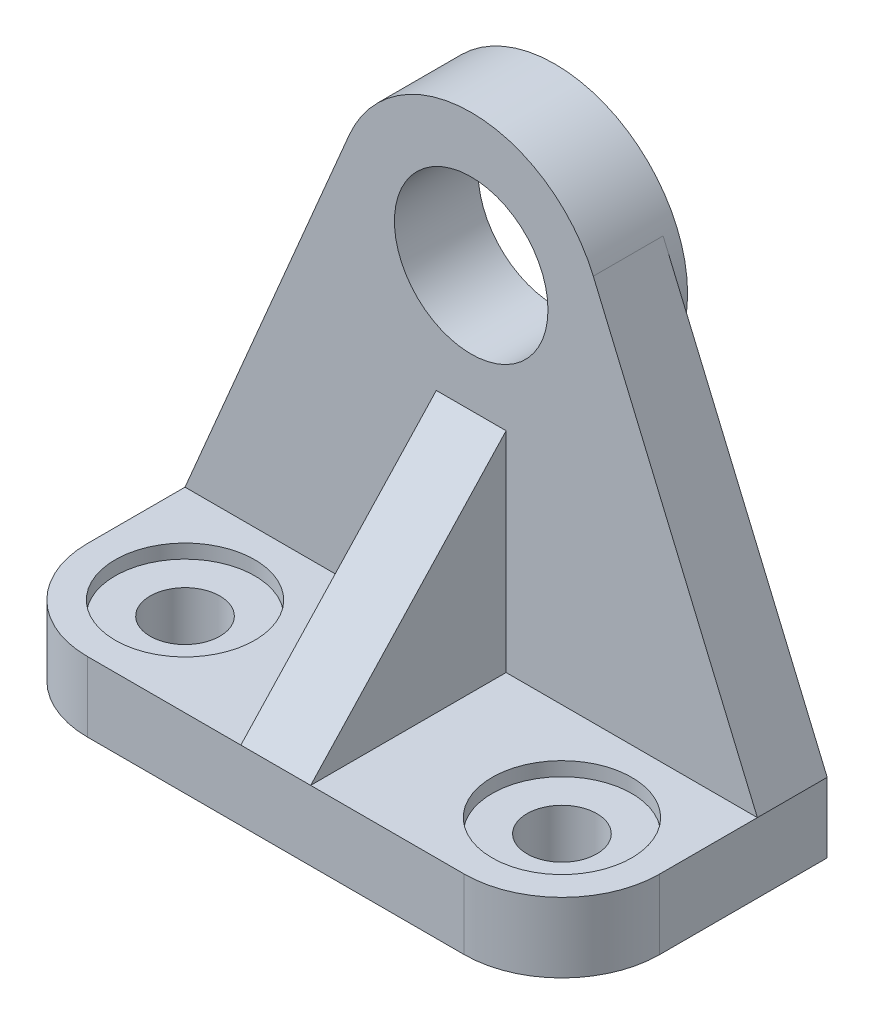
SolidWorks part; units mm, degrees
material "회주철"
ref_plane "정면" through (0, 0, 0) normal (0, 0, 1) x (1, 0, 0)
ref_plane "윗면" through (0, 0, 0) normal (0, 1, 0) x (1, 0, 0)
ref_plane "우측면" through (0, 0, 0) normal (1, 0, 0) x (0, 0, -1)
sketch "스케치1" plane through (0, 0, 0) normal (1, 0, 0) x (0, 0, -1)
  line L0 (0, 0) -> (38, 0)
  line L1 (38, 0) -> (38, 77)
  line L2 (0, 10) -> (28, 10)
  line L3 (28, 10) -> (28, 77)
  line L4 (28, 77) -> (38, 77)
  line L5 (0, 10) -> (0, 0)
  dimension "D1" = 38
  dimension "D2" = 10
  dimension "D3" = 77
extrude "보스-돌출1" add sketch "스케치1" along normal mid plane 82
sketch "스케치2" plane through (0, 0, -28) normal (0, 0, 1) x (1, 0, 0)
  line L0 (-41, 77) -> (-41, 10) construction
  line L1 (-41, 10) -> (-17.4914, 65.4197)
  line L2 (17.4914, 65.4197) -> (41, 10)
  line L3 (-41, 10) -> (-41, 77)
  line L4 (-41, 77) -> (41, 77)
  line L5 (41, 77) -> (41, 10)
  circle A0 centre (0, 58) radius 11
  arc A1 (17.4914, 65.4197) -> (-17.4914, 65.4197) centre (0, 58) ccw
  line M3 (-41, 77) -> (-41, 10)
  line M5 (41, 10) -> (41, 77)
  line M6 (41, 77) -> (-41, 77)
  dimension "D1" = 22
  dimension "D2" = 19
extrude "컷-돌출1" cut sketch "스케치2" against normal blind 82 contours A1 L4 L1 M3 | A1 L2 M5 M6 | A0
sketch "스케치3" plane through (0, 0, 0) normal (1, 0, 0) x (0, 0, -1)
  line L0 (0, 10) -> (28, 10)
  line L1 (28, 10) -> (28, 40)
  line L2 (28, 40) -> (0, 10)
  dimension "D1" = 30
extrude "보스-돌출2" add sketch "스케치3" along normal mid plane 10
fillet "필렛1" radius 14 2 edges at (41, 5, 0) (-41, 5, 0)
sketch "스케치4" plane through (0, 0, 0) normal (0, 1, 0) x (1, 0, 0)
  circle A0 centre (-27, 14) radius 5
  circle A1 centre (27, 14) radius 5
  dimension "D1" = 10
extrude "컷-돌출2" cut sketch "스케치4" along normal up to next
sketch "스케치5" plane through (0, 10, 0) normal (0, 1, 0) x (1, 0, 0)
  circle A0 centre (-27, 14) radius 10
  circle A1 centre (27, 14) radius 10
  dimension "D1" = 20
extrude "컷-돌출3" cut sketch "스케치5" against normal blind 2
sketch "스케치6" plane through (0, 0, -38) normal (0, 0, -1) x (-1, 0, 0)
  circle A0 centre (0, 58) radius 19
  circle A2 centre (0, 58) radius 11
  dimension "D1" = 38
  dimension "D2" = 22
extrude "보스-돌출3" add sketch "스케치6" along normal blind 2
